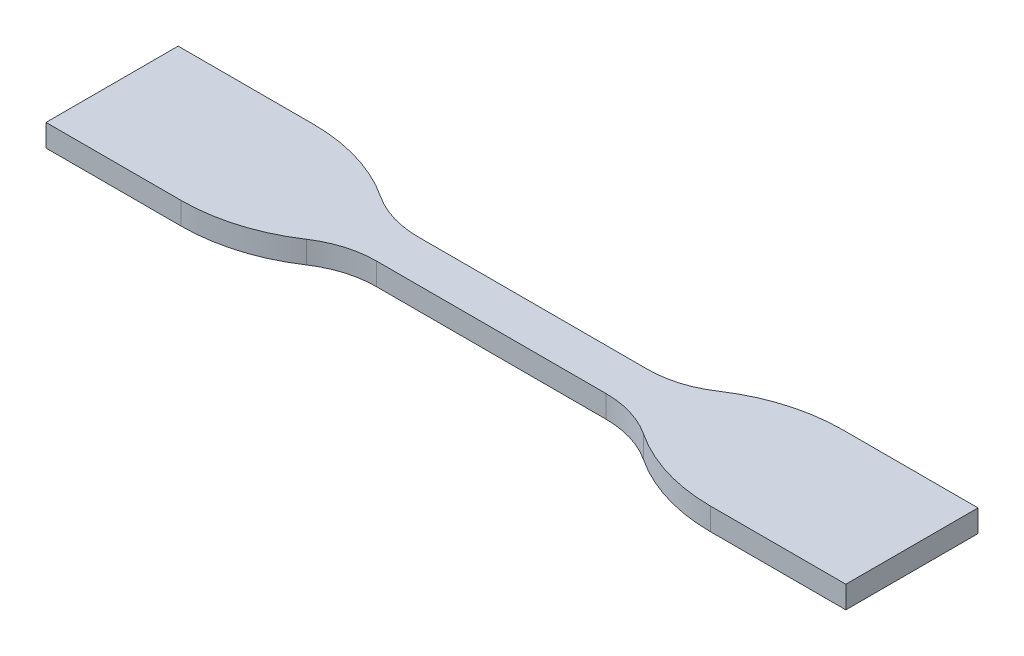
SolidWorks part; units mm, degrees
ref_plane "Front Plane" through (0, 0, 0) normal (0, 0, 1) x (1, 0, 0)
ref_plane "Top Plane" through (0, 0, 0) normal (0, 1, 0) x (1, 0, 0)
ref_plane "Right Plane" through (0, 0, 0) normal (1, 0, 0) x (0, 0, -1)
sketch "Sketch1" plane through (0, 0, 0) normal (0, 1, 0) x (1, 0, 0)
  line L0 (38.0581, -9.5) -> (57.5, -9.5)
  line L1 (-57.5, 9.5) -> (-38.0581, 9.5)
  line L2 (-57.5, 9.5) -> (-57.5, -9.5)
  line L3 (-57.5, -9.5) -> (-38.0581, -9.5)
  line L4 (57.5, 9.5) -> (57.5, -9.5)
  line L5 (0, -9.5) -> (0, 9.5) construction
  line L6 (-57.5, 0) -> (57.5, 0) construction
  line L7 (-16.5, 3) -> (16.5, 3)
  line L9 (-16.5, -3) -> (16.5, -3)
  line L11 (0, -3) -> (0, 3) construction
  line L12 (-16.5, 0) -> (16.5, 0) construction
  line L13 (38.0581, 9.5) -> (57.5, 9.5)
  arc A0 (-16.5, -3) -> (-24.2388, -5.3333) centre (-16.5, -17) ccw
  arc A1 (-24.2388, -5.3333) -> (-38.0581, -9.5) centre (-38.0581, 15.5) cw
  arc A2 (-24.2388, 5.3333) -> (-38.0581, 9.5) centre (-38.0581, -15.5) ccw
  arc A3 (-16.5, 3) -> (-24.2388, 5.3333) centre (-16.5, 17) cw
  arc A4 (24.2388, 5.3333) -> (38.0581, 9.5) centre (38.0581, -15.5) cw
  arc A5 (16.5, 3) -> (24.2388, 5.3333) centre (16.5, 17) ccw
  arc A6 (16.5, -3) -> (24.2388, -5.3333) centre (16.5, -17) cw
  arc A7 (24.2388, -5.3333) -> (38.0581, -9.5) centre (38.0581, 15.5) ccw
  point P0 (0, 0)
  point P4 (0, 0)
  point P12 (-25.1315, -5.9102)
  dimension "D5" = 25
  dimension "D6" = 14
  dimension "D1" = 115
  dimension "D2" = 19
  dimension "D3" = 33
  dimension "D4" = 6
extrude "Boss-Extrude1" add sketch "Sketch1" along normal blind 3.2
